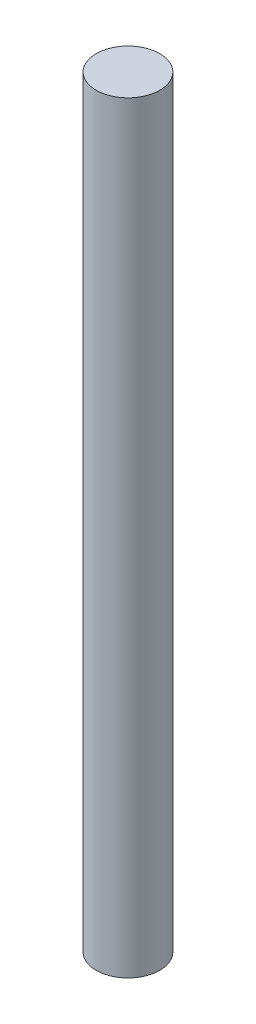
SolidWorks part; units mm, degrees
ref_plane "Front Plane" through (0, 0, 0) normal (0, 0, 1) x (1, 0, 0)
ref_plane "Top Plane" through (0, 0, 0) normal (0, 1, 0) x (1, 0, 0)
ref_plane "Right Plane" through (0, 0, 0) normal (1, 0, 0) x (0, 0, -1)
sketch "Sketch1" plane through (0, 0, 0) normal (0, 1, 0) x (1, 0, 0)
  circle A0 centre (0, 0) radius 6.35
  dimension "D1" = 12.7
extrude "Boss-Extrude1" add sketch "Sketch1" along normal blind 152.4
